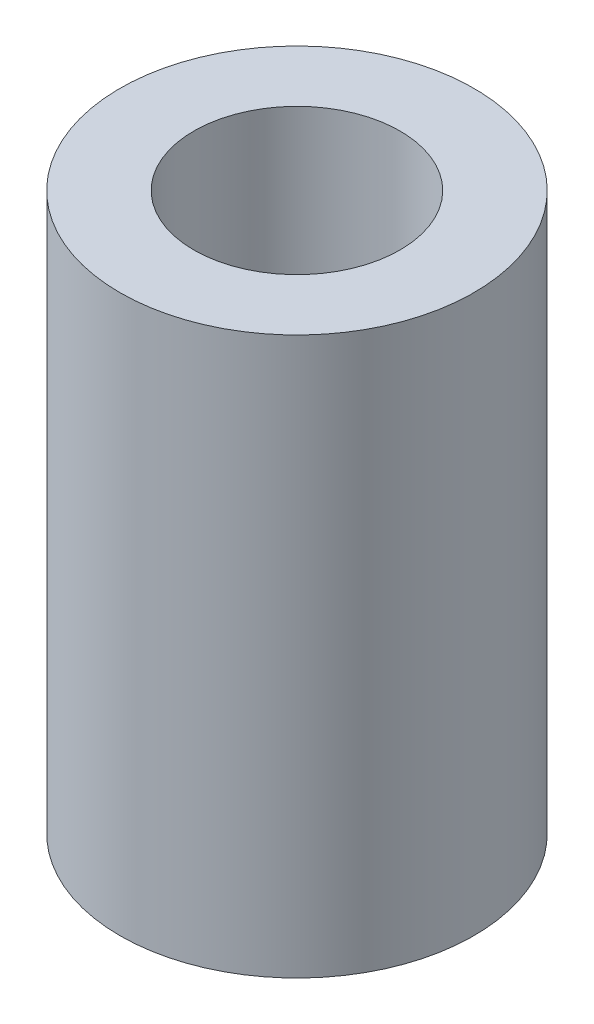
SolidWorks part; units mm, degrees
ref_plane "Top Plane" through (0, 0, 0) normal (0, 0, 1) x (1, 0, 0)
ref_plane "Front Plane" through (0, 0, 0) normal (0, 1, 0) x (1, 0, 0)
ref_plane "Right Plane" through (0, 0, 0) normal (1, 0, 0) x (0, 0, -1)
sketch "Profile Sketch" plane through (0, 0, 0) normal (0, 1, 0) x (1, 0, 0)
  circle A0 centre (0, 0) radius 4.1656
  circle A1 centre (0, 0) radius 7.1501
  dimension "D1" = 8.3312
  dimension "D2" = 14.3002
extrude "Profile Extrude" add sketch "Profile Sketch" along normal blind 22.5
